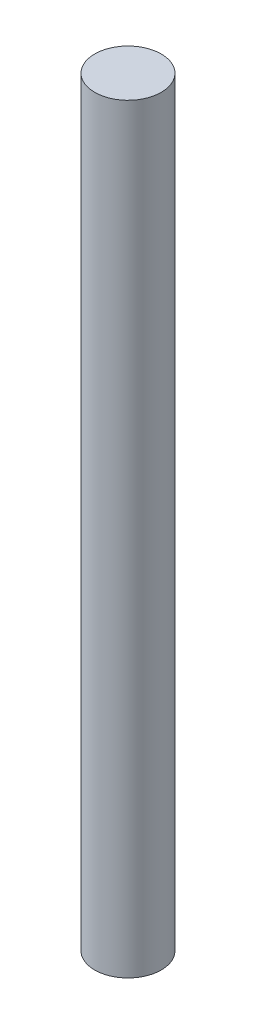
SolidWorks part; units mm, degrees
ref_plane "Спереди" through (0, 0, 0) normal (0, 0, 1) x (1, 0, 0)
ref_plane "Сверху" through (0, 0, 0) normal (0, 1, 0) x (1, 0, 0)
ref_plane "Справа" through (0, 0, 0) normal (1, 0, 0) x (0, 0, -1)
other "Configuration Table"
sketch "Эскиз1" plane through (0, 0, 0) normal (0, 1, 0) x (1, 0, 0)
  circle A0 centre (-1.462, 1.5285) radius 3.5
  dimension "D1" = 7
extrude "Бобышка-Вытянуть1" add sketch "Эскиз1" along normal blind 80
